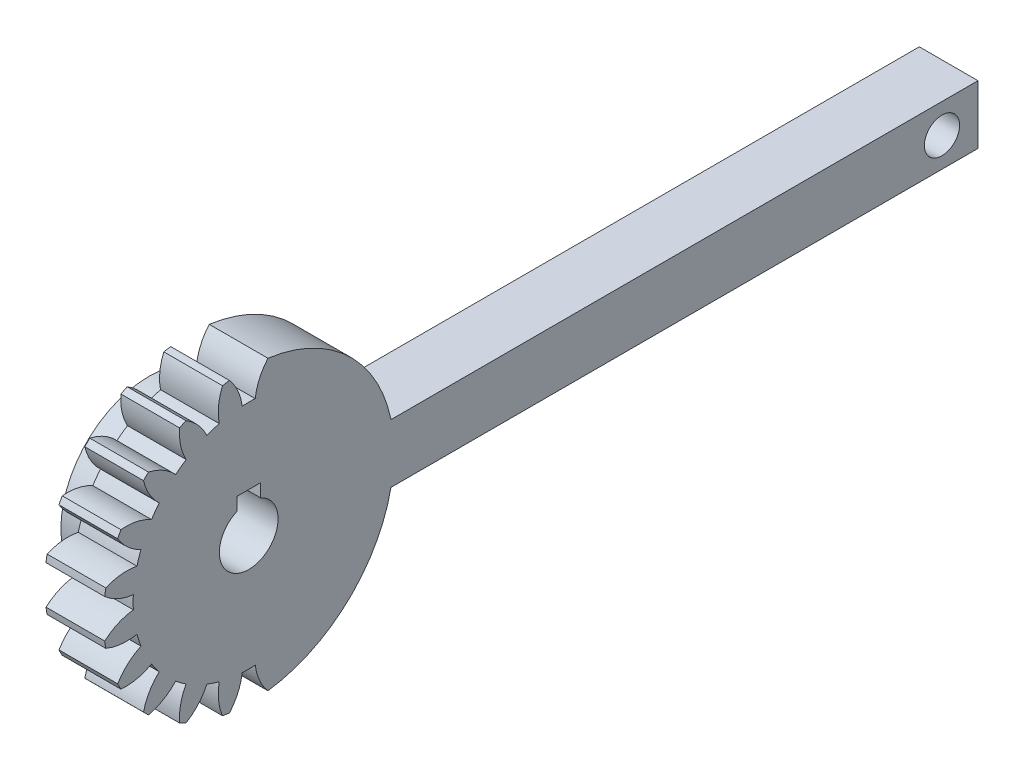
SolidWorks part; units mm, degrees
ref_plane "Plane1" through (0, 0, 0) normal (0, 0, 1) x (1, 0, 0)
ref_plane "Plane2" through (0, 0, 0) normal (0, 1, 0) x (1, 0, 0)
ref_plane "Plane3" through (0, 0, 0) normal (1, 0, 0) x (0, 0, -1)
sketch "HoldingSke" plane through (0, 0, 0) normal (0, 1, 0) x (1, 0, 0)
  line L0 (0, 0) -> (0.4377, -0.0772)
  line L1 (-15, 0) -> (100, 0) construction
  line L2 (0, 0) -> (-2.1039, 2.3779)
  line L3 (0, 0) -> (-11.863, 4.5341)
  line L4 (0, 0) -> (8.1152, 2.9537)
  line L5 (0, 0) -> (-9.3695, -3.4946)
  line L6 (0, 0) -> (-8.2896, -5.593)
  line L7 (-2.1039, 2.3779) -> (0.0486, 12.1435)
  line L8 (-76.2, 54.61) -> (-74.4, 54.61)
  line L9 (-71.009, 38.7566) -> (-53.1078, 45.2721)
  line L10 (-76.2, 71.12) -> (104.1128, 71.12)
  line L11 (0, 0) -> (-10, 0)
  line L12 (-76.2, 101.6) -> (-76.123, 101.6)
  line L13 (24.9733, 27.94) -> (52.9518, 28.4284)
  line L14 (24.9733, 27.94) -> (24.9743, 27.94)
  line L15 (24.9733, 27.94) -> (100.4006, 29.5858)
  line L16 (-63.627, -2.25) -> (-12.827, -2.25)
  circle A0 centre (0, 0) radius 5
  circle A1 centre (0, 0) radius 15
  circle A2 centre (0, 0) radius 15
  circle A3 centre (0, 0) radius 5
  dimension "MHD" = 30
  dimension "Hub_dia" = 30
  dimension "Bore" = 10
  dimension "MBD" = 10
  dimension "Num_teeth" = 20
  dimension "Pitch" = 0.4444
  dimension "Overall_len" = 10
  dimension "Show_teeth" = 10
  dimension "Thickness" = 10
  dimension "OAL" = 10.0001
  dimension "T_dim" = 1.8
  dimension "Ap" = 20
  dimension "H" = 19.05
  dimension "Pitch_radius" = 180.3128
  dimension "Width" = 10
  dimension "Backlash" = 0.077
  dimension "Addendum_fac" = 1
  dimension "Dedendum_fac" = 1.25
  dimension "Clearance_fac" = 0.25
  dimension "Dedendum_add" = 0.001
  dimension "Module" = 2.25
sketch "BasProSke" plane through (0, 0, 0) normal (0, 1, 0) x (1, 0, 0)
  line L0 (-10, 0) -> (60, 0) construction
  line L1 (0, 0) -> (0, 24.75)
  line L2 (0, 0) -> (10, 0)
  line L3 (10, 0) -> (10, 24.75)
  line L4 (10, 24.75) -> (0, 24.75)
  dimension "Thickness" = 10
  dimension "Diameter" = 49.5
revolve "Base-Revolve" add sketch "BasProSke" angle 360 about L0
sketch "TooCutSke" plane through (0, 0, 0) normal (1, 0, 0) x (0, 0, -1)
  line L1 (0, 0) -> (0, 107) construction
  line L2 (0, 0) -> (-1.9, 22.4196) construction
  line L3 (0, 0) -> (-7.021, 44.3291) construction
  line L4 (-1.9, 22.4196) -> (-3.5105, 22.1646) construction
  arc A0 (1.1119, 19.6551) -> (-1.1119, 19.6551) centre (0, 0) ccw
  arc A1 (3.3, 24.5546) -> (-3.3, 24.5546) centre (0, 0) ccw
  circle A2 centre (0, 0) radius 22.5 construction
  circle A3 centre (0, 0) radius 21.1431 construction
  arc A4 (-1.1119, 19.6551) -> (-3.3, 24.5546) centre (-10.0501, 18.6018) ccw
  arc A5 (3.3, 24.5546) -> (1.1119, 19.6551) centre (10.0501, 18.6018) ccw
  dimension "Root_dia" = 39.373
  dimension "Overcut_dia" = 49.5508
  dimension "Pitch_dia" = 45
  dimension "Base_dia" = 42.2862
  dimension "Flank_rad" = 9
  dimension "Half_ang" = 9
  dimension "Half_CT" = 1.6306
extrude "ToothCut" cut sketch "TooCutSke" along normal through all
fillet "Breaks" [suppressed] radius 0.045
fillet "RootFillets" [suppressed] radius 0.5635
pattern_circular "TeethCuts" count 11 every 18 about axis through (-10, 0, 0) along (1, 0, 0) of "ToothCut", "RootFillets", "Breaks"
sketch "HubNeaOneSke" plane through (0, 0, 0) normal (-1, 0, 0) x (0, 0, 1)
  circle A0 centre (0, 0) radius 15
  dimension "Diameter" = 30
extrude "HubNearOne" add sketch "HubNeaOneSke" along normal blind 7.0001
sketch "HubNeaBotSke" plane through (0, 0, 0) normal (-1, 0, 0) x (0, 0, 1)
  circle A0 centre (0, 0) radius 15
  dimension "Diameter" = 30
extrude "HubNearBoth" [suppressed] add sketch "HubNeaBotSke" along normal blind 3.5
ref_plane "FarPln" through (10, 0, 0) normal (1, 0, 0) x (0, 0, -1)
sketch "HubFarSke" plane through (10, 0, 0) normal (1, 0, 0) x (0, 0, -1)
  circle A0 centre (0, 0) radius 15
  dimension "Diameter" = 30
extrude "HubFar" [suppressed] add sketch "HubFarSke" along normal blind 3.5
sketch "BorSke" plane through (0, 0, 0) normal (1, 0, 0) x (0, 0, -1)
  circle A0 centre (0, 0) radius 5
  dimension "Diameter" = 10
extrude "Bore" cut sketch "BorSke" along normal mid plane 20.0001
sketch "KeySke" plane through (0, 0, 0) normal (1, 0, 0) x (0, 0, -1)
  line L0 (-2, 0) -> (-2, 6.8)
  line L1 (-2, 6.8) -> (2, 6.8)
  line L2 (2, 6.8) -> (2, 0)
  line L3 (0, 0) -> (0, 34) construction
  line L4 (-2, 0) -> (2, 0)
  dimension "Offset" = 6.8
  dimension "Width" = 4
extrude "Keyway" cut sketch "KeySke" along normal mid plane 20.0001
pattern_circular "Keyway2" [suppressed] count 2 every 90 about axis through (-10, 0, 0) along (1, 0, 0)
sketch "Esquisse1" plane through (10, 0, 0) normal (1, 0, 0) x (0, 0, -1)
  line L0 (24.2397, -5) -> (24.2397, 5)
  line L1 (24.2397, -5) -> (124.2397, -5)
  line L2 (24.2397, 5) -> (124.2397, 5)
  line L3 (124.2397, -5) -> (124.2397, 5)
  arc A0 (3.2799, -24.5317) -> (3.2799, 24.5317) centre (0, 0) ccw construction
  dimension "D1" = 100
  dimension "D2" = 10
extrude "Boss.-Extru.1" add sketch "Esquisse1" against normal blind 10
sketch "Esquisse2" plane through (0, 0, 0) normal (-1, 0, 0) x (0, 0, 1)
  circle A0 centre (-118.1014, 0) radius 3
  dimension "D1" = 6
extrude "Enlèv. mat.-Extru.2" cut sketch "Esquisse2" against normal blind 10
equation "' \"Module@HoldingSke\" = 6.35"
equation "' \"Num_teeth@HoldingSke\" = 12"
equation "' \"Ap@HoldingSke\" =  20"
equation "' \"Ap@HoldingSke\" = 20"
equation "' \"Width@HoldingSke\" = 0.5 * 25.4"
equation "' \"Hub_dia@HoldingSke\"= 1 * 25.4"
equation "' \"Hub_dia@HoldingSke\" = 1 * 25.4"
equation "' \"Overall_len@HoldingSke\" = 1.0 * 25.4"
equation "' \"Bore@HoldingSke\" = 0.75 * 25.4"
equation "' \"T_dim@HoldingSke\" = 0.1 * 25.4"
equation "' \"Width@KeySke\" = 0.25 * 25.4"
equation "' \"Show_teeth@HoldingSke\" = 13"
equation "' \"Backlash@HoldingSke\" = 0.009 * 25.4"
equation "' \"Addendum_fac@HoldingSke\" = 1.0"
equation "' \"Dedendum_fac@HoldingSke\" = 1.25"
equation "' \"Dedendum_add@HoldingSke\" = 0.00005 * 25.4"
equation "' \"Clearance_fac@HoldingSke\" = 0.25"
equation "\"Pitch@HoldingSke\" = 1 / \"Module@HoldingSke\""
equation "\"Overcut_dia@TooCutSke\" = (\"Num_teeth@HoldingSke\" + 2 * \"Addendum_fac@HoldingSke\") / \"Pitch@HoldingSke\" + 0.002 * 25.4"
equation "\"Pitch_dia@TooCutSke\" = \"Num_teeth@HoldingSke\" / \"Pitch@HoldingSke\""
equation "\"Base_dia@TooCutSke\" = \"Num_teeth@HoldingSke\" / \"Pitch@HoldingSke\" * cos((\"Ap@HoldingSke\"  * 3.14159265 / 180))"
equation "\"Root_dia@TooCutSke\" = (\"Num_teeth@HoldingSke\" + 2) / \"Pitch@HoldingSke\" - 2 * (\"Addendum_fac@HoldingSke\" + \"Dedendum_fac@HoldingSke\") / \"Pitch@HoldingSke\" - \"Dedendum_add@HoldingSke\" * 2"
equation "\"Half_ang@TooCutSke\" = 180 / \"Num_teeth@HoldingSke\""
equation "\"Half_CT@TooCutSke\" = \"Num_teeth@HoldingSke\" / \"Pitch@HoldingSke\" * sin((3.14159265 / 2 / \"Num_teeth@HoldingSke\")) / 2 - 7 * \"Backlash@HoldingSke\" / 4"
equation "\"Flank_rad@TooCutSke\" = \"Num_teeth@HoldingSke\" / \"Pitch@HoldingSke\" / 5"
equation "\"Radius@RootFillets\" = \"Clearance_fac@HoldingSke\" / \"Pitch@HoldingSke\" + \"Dedendum_add@HoldingSke\""
equation "\"Break_rad@Breaks\" = 0.02 / \"Pitch@HoldingSke\""
equation "\"Thickness@HoldingSke\" = \"Width@HoldingSke\""
equation "\"OAL@HoldingSke\" = \"Thickness@HoldingSke\""
equation "\"MHD@HoldingSke\" = (\"Num_teeth@HoldingSke\" + 2) / \"Pitch@HoldingSke\" - 2 * (\"Addendum_fac@HoldingSke\" + \"Dedendum_fac@HoldingSke\")  / \"Pitch@HoldingSke\" - \"Dedendum_add@HoldingSke\" * 2"
equation "\"MBD@HoldingSke\" = (\"Num_teeth@HoldingSke\" + 2) / \"Pitch@HoldingSke\" - 2 * (\"Addendum_fac@HoldingSke\" + \"Dedendum_fac@HoldingSke\")  / \"Pitch@HoldingSke\" - \"Dedendum_add@HoldingSke\" * 2 - 0.002 * 25.4"
equation "\"MHD@HoldingSke\" = ((sgn( \"MHD@HoldingSke\" - \"Hub_dia@HoldingSke\" )-1)*( \"MHD@HoldingSke\" - \"Hub_dia@HoldingSke\" ))/-2+ \"Hub_dia@HoldingSke\""
equation "\"MBD@HoldingSke\" = ((sgn( \"MBD@HoldingSke\" - \"Bore@HoldingSke\" )-1)*( \"MBD@HoldingSke\" - \"Bore@HoldingSke\" ))/-2+ \"Bore@HoldingSke\""
equation "\"OAL@HoldingSke\" = ((sgn( \"OAL@HoldingSke\" - \"Overall_len@HoldingSke\" )+1)*( \"OAL@HoldingSke\" - \"Overall_len@HoldingSke\" ))/2 + \"Overall_len@HoldingSke\" + 0.000002 * 25.4"
equation "\"Num_teeth@TeethCuts\" = int( \"Show_teeth@HoldingSke\" ) + 1"
equation "\"Num_teeth@TeethCuts\" = ((sgn( \"Num_teeth@TeethCuts\" - \"Num_teeth@HoldingSke\" )-1)*( \"Num_teeth@TeethCuts\" - \"Num_teeth@HoldingSke\" ))/-2+ \"Num_teeth@HoldingSke\""
equation "\"Num_teeth@TeethCuts\" = ((sgn( \"Num_teeth@TeethCuts\" - 2.0)+1)*( \"Num_teeth@TeethCuts\" - 2.0))/2 +2.0"
equation "\"Angle@TeethCuts\" = 360.0 / \"Num_teeth@HoldingSke\""
equation "\"Diameter@BasProSke\" = (\"Num_teeth@HoldingSke\" + 2 * \"Addendum_fac@HoldingSke\") / \"Pitch@HoldingSke\""
equation "\"Thickness@BasProSke\"  = \"Thickness@HoldingSke\""
equation "' \"Fillet_rad@BasProSke\" =  \"Thickness@HoldingSke\" * 0.05"
equation "' \"Fillet_rad@BasProSke\" = \"Thickness@HoldingSke\" * 0.05"
equation "\"MHD@HoldingSke\" = ((sgn( \"MHD@HoldingSke\" - \"Root_dia@TooCutSke\" )-1)*( \"MHD@HoldingSke\" - \"Root_dia@TooCutSke\" ))/-2+ \"Root_dia@TooCutSke\""
equation "\"Diameter@HubNeaOneSke\" = \"MHD@HoldingSke\""
equation "\"Length@HubNearOne\" = \"OAL@HoldingSke\" - \"Thickness@BasProSke\""
equation "\"Diameter@HubNeaBotSke\" = \"MHD@HoldingSke\""
equation "\"Length@HubNearBoth\" = ( \"OAL@HoldingSke\" - \"Thickness@BasProSke\" ) / 2.0"
equation "\"Thickness@FarPln\" = \"Thickness@BasProSke\""
equation "\"Diameter@HubFarSke\" = \"MHD@HoldingSke\""
equation "\"Length@HubFar\" = ( \"OAL@HoldingSke\" - \"Thickness@BasProSke\" ) / 2.0"
equation "\"Diameter@BorSke\" = \"MBD@HoldingSke\""
equation "\"D1@Bore\" = \"OAL@HoldingSke\" * 2.0"
equation "\"D1@Keyway\" = \"OAL@HoldingSke\" * 2.0"
equation "\"Offset@KeySke\" = \"T_dim@HoldingSke\" + \"MBD@HoldingSke\" / 2.0"
